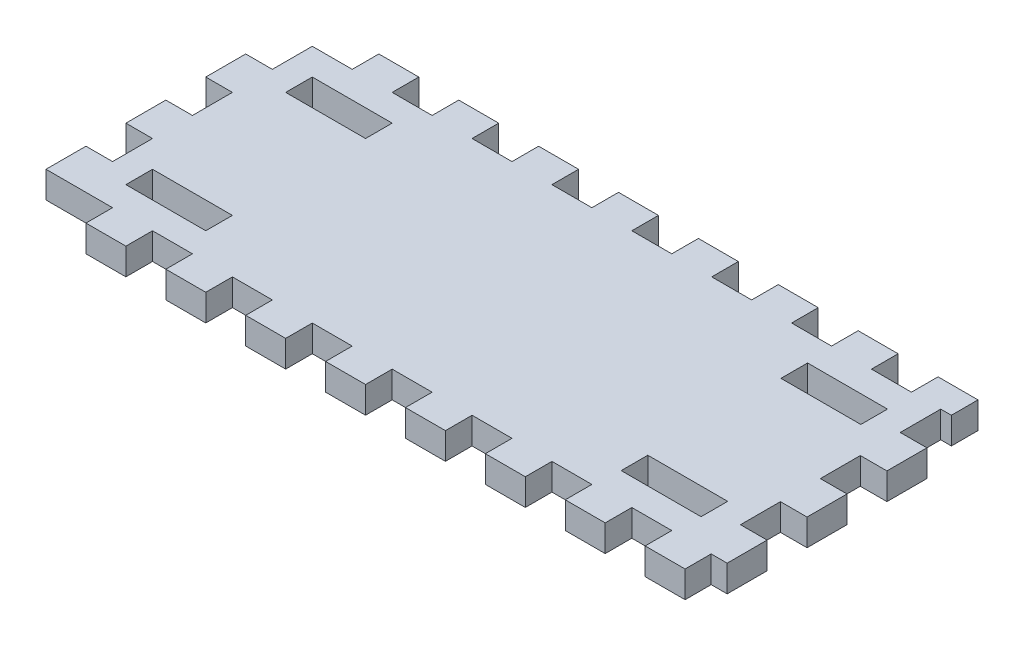
SolidWorks part; units mm, degrees
material "Pine"
ref_plane "Front Plane" through (0, 0, 0) normal (0, 0, 1) x (1, 0, 0)
ref_plane "Top Plane" through (0, 0, 0) normal (0, 1, 0) x (1, 0, 0)
ref_plane "Right Plane" through (0, 0, 0) normal (1, 0, 0) x (0, 0, -1)
sketch "Sketch1" plane through (0, 0, 0) normal (0, 1, 0) x (1, 0, 0)
  line L0 (6.35, -44.45) -> (25.4, -44.45)
  line L1 (0, 0) -> (149.86, 0)
  line L2 (0, 0) -> (0, -57.15)
  line L3 (0, -57.15) -> (149.86, -57.15)
  line L4 (149.86, 0) -> (149.86, -57.15)
  line L5 (6.35, -6.35) -> (25.4, -6.35)
  line L6 (6.35, -6.35) -> (6.35, -12.7)
  line L7 (6.35, -12.7) -> (25.4, -12.7)
  line L8 (25.4, -6.35) -> (25.4, -12.7)
  line L9 (6.35, -44.45) -> (6.35, -50.8)
  line L10 (6.35, -50.8) -> (25.4, -50.8)
  line L11 (25.4, -44.45) -> (25.4, -50.8)
  line L12 (124.46, -44.45) -> (143.51, -44.45)
  line L13 (124.46, -44.45) -> (124.46, -50.8)
  line L14 (124.46, -50.8) -> (143.51, -50.8)
  line L15 (143.51, -44.45) -> (143.51, -50.8)
  line L16 (124.46, -6.35) -> (143.51, -6.35)
  line L17 (124.46, -6.35) -> (124.46, -12.7)
  line L18 (124.46, -12.7) -> (143.51, -12.7)
  line L19 (143.51, -6.35) -> (143.51, -12.7)
  dimension "D1" = 149.86
  dimension "D2" = 57.15
  dimension "D3" = 19.05
  dimension "D4" = 6.35
  dimension "D5" = 6.35
  dimension "D6" = 6.35
  dimension "D7" = 19.05
  dimension "D8" = 6.35
  dimension "D9" = 19.05
  dimension "D10" = 6.35
  dimension "D11" = 19.05
  dimension "D12" = 6.35
  dimension "D13" = 6.35
  dimension "D14" = 6.35
  dimension "D15" = 6.35
  dimension "D16" = 6.35
  dimension "D17" = 6.35
  dimension "D18" = 6.35
extrude "Boss-Extrude1" add sketch "Sketch1" along normal blind 6.35
sketch "Sketch2" plane through (0, 0, 0) normal (0, -1, 0) x (1, 0, 0)
  line L0 (0, 0) -> (0, 57.15) construction
  line L1 (0, 9.525) -> (-6.35, 9.525)
  line L2 (0, 9.525) -> (0, 19.05)
  line L3 (0, 19.05) -> (-6.35, 19.05)
  line L4 (-6.35, 9.525) -> (-6.35, 19.05)
  line L5 (149.86, 0) -> (0, 0) construction
  line L6 (0, 28.575) -> (0, 38.1)
  line L7 (0, 28.575) -> (-6.35, 28.575)
  line L8 (-6.35, 28.575) -> (-6.35, 38.1)
  line L9 (0, 38.1) -> (-6.35, 38.1)
  line L10 (0, 47.625) -> (0, 57.15)
  line L11 (0, 47.625) -> (-6.35, 47.625)
  line L12 (-6.35, 47.625) -> (-6.35, 57.15)
  line L13 (0, 57.15) -> (-6.35, 57.15)
  line L18 (149.86, 28.575) -> (0, 28.575) construction
  line L19 (0, 57.15) -> (149.86, 57.15) construction
  line L20 (149.86, 57.15) -> (149.86, 0) construction
  line L21 (149.86, 19.177) -> (156.21, 19.177)
  line L22 (149.86, 19.177) -> (149.86, 9.652)
  line L23 (149.86, 9.652) -> (156.21, 9.652)
  line L24 (156.21, 19.177) -> (156.21, 9.652)
  line L37 (28.575, 57.15) -> (28.575, 63.5)
  line L38 (9.525, 57.15) -> (19.05, 57.15)
  line L39 (9.525, 57.15) -> (9.525, 63.5)
  line L40 (9.525, 63.5) -> (19.05, 63.5)
  line L41 (19.05, 57.15) -> (19.05, 63.5)
  line L42 (28.575, 57.15) -> (38.1, 57.15)
  line L43 (38.1, 57.15) -> (38.1, 63.5)
  line L44 (28.575, 63.5) -> (38.1, 63.5)
  line L45 (47.625, 57.15) -> (47.625, 63.5)
  line L46 (47.625, 57.15) -> (57.15, 57.15)
  line L47 (57.15, 57.15) -> (57.15, 63.5)
  line L48 (47.625, 63.5) -> (57.15, 63.5)
  line L49 (66.675, 57.15) -> (66.675, 63.5)
  line L50 (66.675, 57.15) -> (76.2, 57.15)
  line L51 (76.2, 57.15) -> (76.2, 63.5)
  line L52 (66.675, 63.5) -> (76.2, 63.5)
  line L53 (85.725, 57.15) -> (85.725, 63.5)
  line L54 (85.725, 57.15) -> (95.25, 57.15)
  line L55 (95.25, 57.15) -> (95.25, 63.5)
  line L56 (85.725, 63.5) -> (95.25, 63.5)
  line L57 (104.775, 57.15) -> (104.775, 63.5)
  line L58 (104.775, 57.15) -> (114.3, 57.15)
  line L59 (114.3, 57.15) -> (114.3, 63.5)
  line L60 (104.775, 63.5) -> (114.3, 63.5)
  line L61 (123.825, 57.15) -> (123.825, 63.5)
  line L62 (123.825, 57.15) -> (133.35, 57.15)
  line L63 (133.35, 57.15) -> (133.35, 63.5)
  line L64 (123.825, 63.5) -> (133.35, 63.5)
  line L65 (142.875, 57.15) -> (142.875, 63.5)
  line L66 (142.875, 57.15) -> (152.4, 57.15)
  line L67 (152.4, 57.15) -> (152.4, 63.5)
  line L68 (142.875, 63.5) -> (152.4, 63.5)
  line L101 (0, 76.2) -> (-6.35, 76.2) [skipped]
  line L102 (-6.35, 66.675) -> (-6.35, 76.2) [skipped]
  line L103 (0, 66.675) -> (-6.35, 66.675) [skipped]
  line L104 (0, 66.675) -> (0, 76.2) [skipped]
  line L105 (9.525, -6.35) -> (19.05, -6.35)
  line L106 (19.05, 0) -> (19.05, -6.35)
  line L107 (9.525, 0) -> (19.05, 0)
  line L108 (9.525, 0) -> (9.525, -6.35)
  line L109 (142.875, 0) -> (152.4, 0)
  line L110 (152.4, 0) -> (152.4, -6.35)
  line L111 (142.875, -6.35) -> (152.4, -6.35)
  line L112 (142.875, 0) -> (142.875, -6.35)
  line L113 (123.825, 0) -> (133.35, 0)
  line L114 (133.35, 0) -> (133.35, -6.35)
  line L115 (123.825, -6.35) -> (133.35, -6.35)
  line L116 (123.825, 0) -> (123.825, -6.35)
  line L117 (104.775, 0) -> (114.3, 0)
  line L118 (114.3, 0) -> (114.3, -6.35)
  line L119 (104.775, -6.35) -> (114.3, -6.35)
  line L120 (104.775, 0) -> (104.775, -6.35)
  line L121 (85.725, 0) -> (95.25, 0)
  line L122 (95.25, 0) -> (95.25, -6.35)
  line L123 (85.725, -6.35) -> (95.25, -6.35)
  line L124 (85.725, 0) -> (85.725, -6.35)
  line L125 (66.675, 0) -> (76.2, 0)
  line L126 (76.2, 0) -> (76.2, -6.35)
  line L127 (66.675, -6.35) -> (76.2, -6.35)
  line L128 (66.675, 0) -> (66.675, -6.35)
  line L129 (47.625, 0) -> (57.15, 0)
  line L130 (57.15, 0) -> (57.15, -6.35)
  line L131 (47.625, -6.35) -> (57.15, -6.35)
  line L132 (47.625, 0) -> (47.625, -6.35)
  line L133 (28.575, 0) -> (38.1, 0)
  line L134 (38.1, 0) -> (38.1, -6.35)
  line L135 (28.575, -6.35) -> (38.1, -6.35)
  line L136 (28.575, 0) -> (28.575, -6.35)
  line L137 (149.86, 38.227) -> (149.86, 28.702)
  line L138 (149.86, 38.227) -> (156.21, 38.227)
  line L139 (156.21, 38.227) -> (156.21, 28.702)
  line L140 (149.86, 28.702) -> (156.21, 28.702)
  line L141 (149.86, 57.277) -> (149.86, 47.752)
  line L142 (149.86, 57.277) -> (156.21, 57.277)
  line L143 (156.21, 57.277) -> (156.21, 47.752)
  line L144 (149.86, 47.752) -> (156.21, 47.752)
  dimension "D1" = 6.35
  dimension "D2" = 9.525
  dimension "D3" = 9.525
  dimension "D5" = 6.35
  dimension "D6" = 9.652
  dimension "D7" = 9.525
  dimension "D8" = 9.525
  dimension "D10" = 6.35
  dimension "D11" = 9.525
  dimension "D12" = 3
  dimension "D14" = 9.525
  dimension "D9" = 9.525
  dimension "D15" = 9.525
  dimension "D4" = 4
  dimension "D13" = 8
extrude "Boss-Extrude2" add sketch "Sketch2" against normal up to surface (6.35 mm away)
